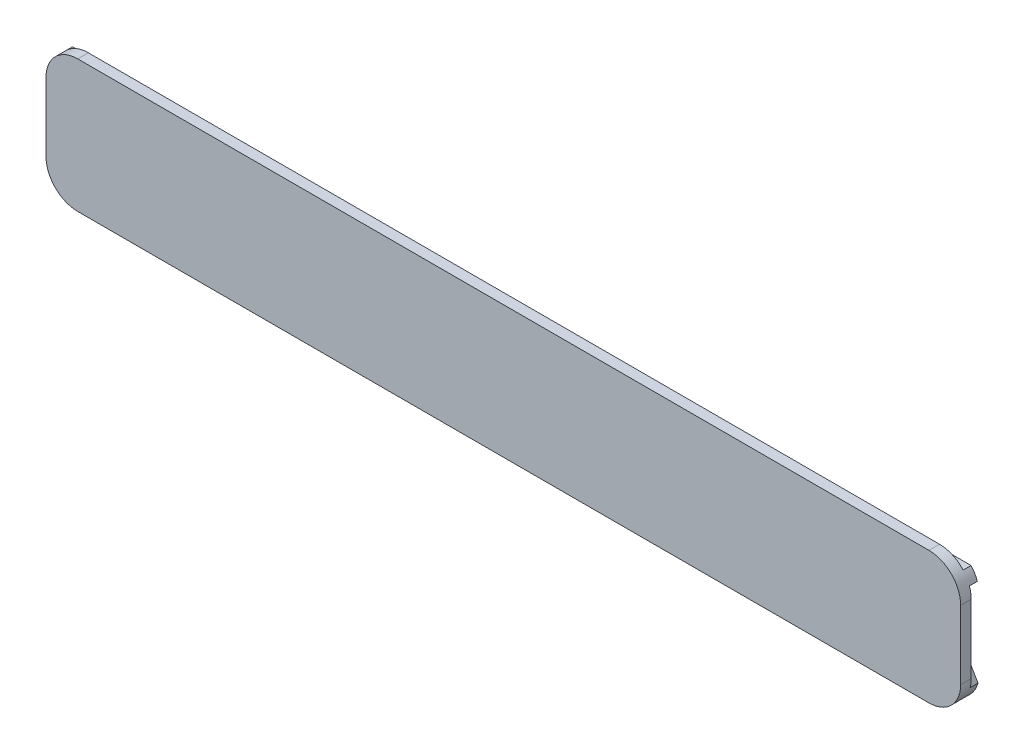
SolidWorks part; units mm, degrees
ref_plane "Front Plane" through (0, 0, 0) normal (0, 0, 1) x (1, 0, 0)
ref_plane "Top Plane" through (0, 0, 0) normal (0, 1, 0) x (1, 0, 0)
ref_plane "Right Plane" through (0, 0, 0) normal (1, 0, 0) x (0, 0, -1)
sketch "Sketch1" plane through (0, 0, 0) normal (0, 0, 1) x (1, 0, 0)
  line L0 (0, 0) -> (55.7, 0) construction
  line L1 (-58.65, 12.5) -> (114.35, 12.5)
  line L2 (-58.65, 12.5) -> (-58.65, -12.5)
  line L3 (-58.65, -12.5) -> (114.35, -12.5)
  line L4 (114.35, 12.5) -> (114.35, -12.5)
  circle A0 centre (55.7, 0) radius 3 construction
  circle A1 centre (0, 0) radius 3 construction
  circle A2 centre (55.7, 0) radius 3 construction
  circle A3 centre (0, 0) radius 3 construction
  circle A4 centre (0, 0) radius 3.2
  circle A5 centre (55.7, 0) radius 3.2
  point P14 (27.85, 0)
  point P15 (27.85, 12.5)
  point P16 (114.35, 0)
  dimension "D2" = 25
  dimension "D3" = 173
  dimension "D1" = 0.2
extrude "Boss-Extrude1" add sketch "Sketch1" against normal blind 1
sketch "Sketch2" plane through (0, 0, 0) normal (0, 0, 1) x (1, 0, 0)
  line L4 (-58.65, 12.5) -> (-58.65, -12.5)
  line L5 (-58.65, -12.5) -> (114.35, -12.5)
  line L6 (114.35, -12.5) -> (114.35, 12.5)
  line L7 (114.35, 12.5) -> (-58.65, 12.5)
  line L8 (-58.65, 12.5) -> (-58.65, -12.5)
  line L9 (-58.65, -12.5) -> (114.35, -12.5)
  line L10 (114.35, -12.5) -> (114.35, 12.5)
  line L11 (114.35, 12.5) -> (-58.65, 12.5)
  dimension "D1" = 0
extrude "Boss-Extrude2" add sketch "Sketch2" along normal blind 1
sketch "Sketch6" plane through (0, 0, -1) normal (0, 0, -1) x (-1, 0, 0)
  circle A0 centre (0, 0) radius 3.2 construction
  circle A1 centre (-55.7, 0) radius 3.2 construction
  circle A2 centre (0, 0) radius 3.2
  circle A3 centre (-55.7, 0) radius 3.2
  circle A4 centre (-55.7, 0) radius 5.2
  circle A5 centre (0, 0) radius 5.2
  dimension "D1" = 2
extrude "Boss-Extrude5" add sketch "Sketch6" along normal blind 2.5
sketch "Sketch5" plane through (0, 0, -1) normal (0, 0, -1) x (-1, 0, 0)
  line L0 (-105.35, 0) -> (49894.65, 0) construction
  line L1 (-114.35, -12.5) -> (-114.35, 12.5) construction
  line L2 (58.65, 12.5) -> (58.65, -12.5) construction
  line L3 (-27.85, -10.5) -> (-27.85, -8.5)
  line L4 (-114.35, 10.5) -> (-27.85, 10.5)
  line L5 (-114.35, 10.5) -> (-114.35, 8.5)
  line L6 (-114.35, 8.5) -> (-104.535, 8.5)
  line L7 (-27.85, 10.5) -> (-27.85, 8.5)
  line L8 (-112.0406, -8.5) -> (-90.4107, -8.5)
  line L9 (-114.35, -10.5) -> (-114.35, -8.5)
  line L10 (-114.35, -10.5) -> (-27.85, -10.5)
  line L11 (-114.35, 12.5) -> (58.65, 12.5) construction
  line L12 (-114.35, -8.5) -> (-104.535, 8.5)
  line L13 (-102.2256, 8.5) -> (-100.2256, 8.5)
  line L14 (-97.9162, 8.5) -> (-88.1013, -8.5)
  line L15 (-88.1013, -8.5) -> (-86.1013, -8.5)
  line L16 (-83.7919, -8.5) -> (-73.9769, 8.5)
  line L17 (-112.0406, -8.5) -> (-102.2256, 8.5)
  line L18 (-102.2256, 8.5) -> (-100.2256, 8.5)
  line L19 (-100.2256, 8.5) -> (-90.4107, -8.5)
  line L20 (-86.1013, -8.5) -> (-76.2863, 8.5)
  line L21 (-40.9744, 8.5) -> (-31.1594, -8.5)
  line L23 (-28.85, -8.5) -> (-38.665, 8.5)
  line L25 (-102.2256, 8.5) -> (-100.2256, 8.5)
  line L26 (-97.9162, 8.5) -> (-76.2863, 8.5)
  line L27 (-88.1013, -8.5) -> (-86.1013, -8.5)
  line L28 (-83.7919, -8.5) -> (-49.6, -8.5)
  line L29 (-73.9769, 8.5) -> (-45.0449, 8.5)
  line L30 (-38.665, 8.5) -> (-27.85, 8.5)
  line L31 (-28.85, -8.5) -> (-27.85, -8.5)
  line L32 (-45.0449, 8.5) -> (-49.6, -8.5)
  line L34 (-47.5295, -8.5) -> (-42.9744, 8.5)
  line L35 (-42.9744, 8.5) -> (-40.9744, 8.5)
  line L36 (-47.5295, -8.5) -> (-31.1594, -8.5)
  point P4 (-114.35, 0)
  point P7 (58.65, 0)
  point P34 (-27.85, 12.5)
  line M32 (-114.35, 12.5) -> (-114.35, -12.5)
  dimension "D1" = 2
  dimension "D2" = 2
  dimension "D3" = 2
  dimension "D4" = 2
  dimension "D5" = 2
  dimension "D6" = 2
  dimension "D7" = 60
  dimension "D8" = 2
  dimension "D9" = 1
  dimension "D10" = 2
  dimension "D11" = 45
extrude "Boss-Extrude4" add sketch "Sketch5" along normal blind 1.5 contours L12 L0 L17 L13 L19 L14 L26 L20 L16 L29 L21 L23 L30 L7 L4 L6 M32 | L0 L12 L10 L3 L31 L23 L21 L28 L16 L20 L15 L14 L19 L8 L17 M32
ref_plane "Plane1" through (27.85, 0, 0) normal (1, 0, 0) x (0, 0, -1)
mirror "Mirror1" about plane through (27.85, 0, 0) normal (1, 0, 0) of "Boss-Extrude4"
fillet "Fillet1" radius 6 4 edges at (114.35, 12.5, 0) (114.35, -12.5, 0) (-58.65, -12.5, 0) (-58.65, 12.5, 0)
sketch "Sketch3" plane through (0, 0, 1) normal (0, 0, 1) x (1, 0, 0)
  line L0 (-58.65, -5) -> (114.35, -5) construction
  line L1 (-52.65, -12.5) -> (108.35, -12.5) construction
  line L2 (-58.65, 6.5) -> (-58.65, -6.5) construction
  text T0 "ED Robotics" font "Century Gothic" height 10
  point P7 (27.85, -12.5)
  point P8 (27.85, -5)
  dimension "D1" = 5
extrude "Engraved team name" [suppressed] cut sketch "Sketch3" against normal blind 0.5
equation "\"D3@Sketch5\"=\"D1@Sketch5\""
equation "\"D4@Sketch5\"=\"D3@Sketch5\""
equation "\"D5@Sketch5\"=\"D3@Sketch5\""
equation "\"D6@Sketch5\"=\"D3@Sketch5\""
equation "\"D8@Sketch5\"=\"D3@Sketch5\""
equation "\"D9@Sketch5\"=\"D3@Sketch5\"/2"
equation "\"D10@Sketch5\"=\"D3@Sketch5\""
